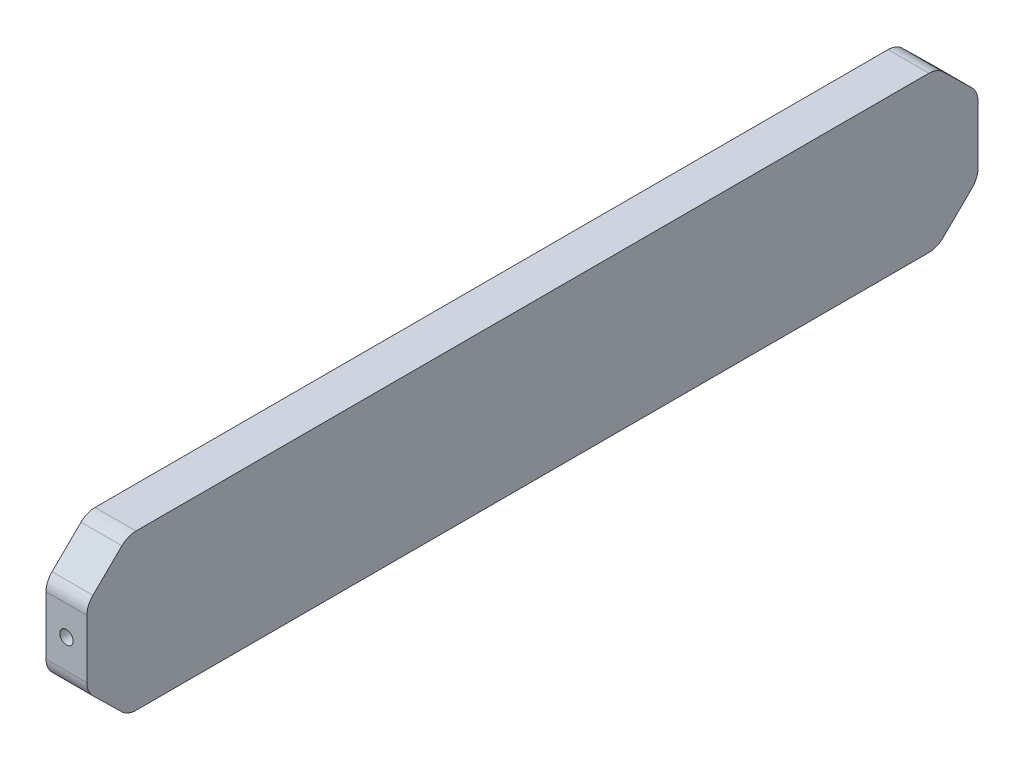
SolidWorks part; units mm, degrees
ref_plane "Front Plane" through (0, 0, 0) normal (0, 0, 1) x (1, 0, 0)
ref_plane "Top Plane" through (0, 0, 0) normal (0, 1, 0) x (1, 0, 0)
ref_plane "Right Plane" through (0, 0, 0) normal (1, 0, 0) x (0, 0, -1)
sketch "Sketch1" plane through (0, 0, 0) normal (0, 1, 0) x (1, 0, 0)
  line L1 (0, 0) -> (10, 0)
  line L2 (0, 0) -> (0, 218)
  line L3 (0, 218) -> (10, 218)
  line L4 (10, 0) -> (10, 218)
  dimension "D1" = 218
  dimension "D2" = 10
extrude "Boss-Extrude1" add sketch "Sketch1" along normal blind 38
sketch "Sketch3" plane through (0, 0, 0) normal (1, 0, 0) x (0, 0, -1)
  line L0 (218, 38) -> (208, 38)
  line L1 (218, 38) -> (0, 38) construction
  line L2 (208, 38) -> (218, 28.202)
  line L3 (218, 38) -> (218, 0) construction
  line L4 (218, 28.202) -> (218, 38)
  line L5 (262.958, 19) -> (-29.335, 19) construction
  line L6 (218, 9.798) -> (218, 0)
  line L7 (218, 0) -> (208, 0)
  line L8 (208, 0) -> (218, 9.798)
  line L9 (109, 74.2488) -> (109, -32.272) construction
  line L10 (0, 38) -> (0, 0) construction
  line L11 (0, 0) -> (10, 0)
  line L12 (0, 9.798) -> (0, 0)
  line L13 (10, 0) -> (0, 9.798)
  line L14 (0, 28.202) -> (0, 38)
  line L15 (0, 38) -> (10, 38)
  line L16 (10, 38) -> (0, 28.202)
  dimension "D1" = 10
  dimension "D2" = 9.798
  dimension "D3" = 19
  dimension "D4" = 109
extrude "Cut-Extrude1" cut sketch "Sketch3" along normal through all
fillet "Fillet1" radius 4.92 8 edges at (5, 0, -10) (5, 9.798, 0) (5, 28.202, 0) (5, 38, -10) (5, 0, -208) (5, 9.798, -218) (5, 28.202, -218) (5, 38, -208)
sketch "Sketch5" plane through (0, 0, 0) normal (0, 0, 1) x (1, 0, 0)
  line L0 (10, 0) -> (0, 0) construction
  line L1 (0, 26.1346) -> (0, 11.8654) construction
  circle A0 centre (5, 19) radius 1.651
  dimension "D1" = 3.302
  dimension "D2" = 19
  dimension "D3" = 5
hole_wizard "#30 (0.1285) Diameter Hole1" positions "Sketch6" profile "Sketch7" hole size "#30" standard "ANSI Inch"
sketch "Sketch6" plane through (0, 0, 0) normal (0, 0, 1) x (1, 0, 0)
  point P0 (5, 19)
sketch "Sketch7" plane through (5, 19, 0) normal (1, 0, 0) x (0, -1, 0)
  line L0 (0, 0) -> (0, 10.9806)
  line L1 (0, 10.9806) -> (1.6319, 10)
  line L2 (1.6319, 10) -> (1.6319, 0)
  line L5 (1.6319, 0) -> (0, 0)
  line L10 (0, 10.9806) -> (-1.632, 10) construction
  line L11 (0, -6.35) -> (0, 107.95) construction
  dimension "Hole Dia." = 3.2639
  dimension "Hole Depth" = 10
  dimension "Drill Angle" = 118
hole_wizard "#30 (0.1285) Diameter Hole2" positions "Sketch8" profile "Sketch9" hole size "#30" standard "ANSI Inch"
sketch "Sketch8" plane through (0, 0, -218) normal (0, 0, -1) x (-1, 0, 0)
  line L0 (0, 0) -> (-10, 0) construction
  line L2 (0, 26.1346) -> (0, 11.8654) construction
  point P0 (-5, 19)
  point P9 (-10, 19.3414)
  dimension "D1" = 19
  dimension "D2" = 5
sketch "Sketch9" plane through (5, 19, -218) normal (1, 0, 0) x (0, 1, 0)
  line L0 (0, 0) -> (0, 10.8866)
  line L1 (0, 10.8866) -> (1.6319, 9.906)
  line L2 (1.6319, 9.906) -> (1.6319, 0)
  line L5 (1.6319, 0) -> (0, 0)
  line L10 (0, 10.8866) -> (-1.632, 9.906) construction
  line L11 (0, -6.35) -> (0, 107.95) construction
  dimension "Hole Dia." = 3.2639
  dimension "Hole Depth" = 9.906
  dimension "Drill Angle" = 118
